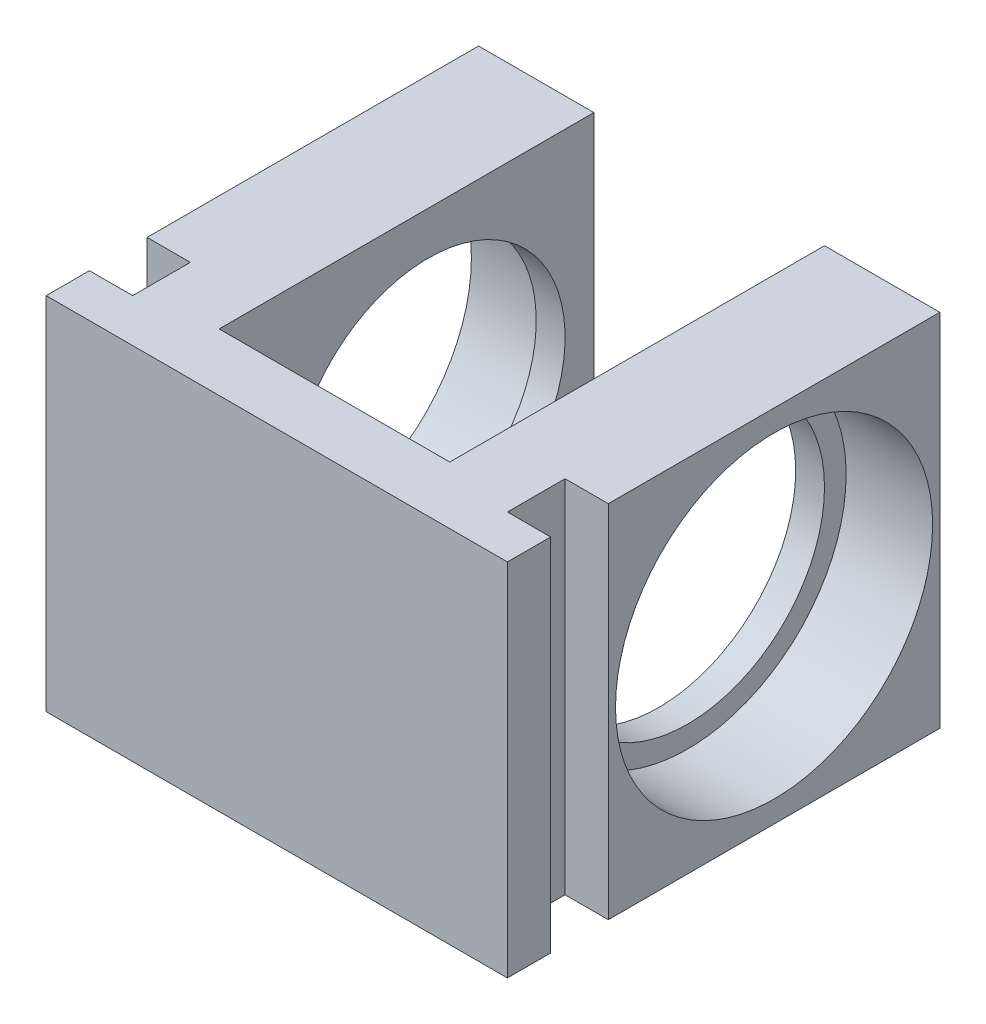
SolidWorks part; units mm, degrees
ref_plane "Ebene vorne" through (0, 0, 0) normal (0, 0, 1) x (1, 0, 0)
ref_plane "Ebene oben" through (0, 0, 0) normal (0, 1, 0) x (1, 0, 0)
ref_plane "Ebene rechts" through (0, 0, 0) normal (1, 0, 0) x (0, 0, -1)
sketch "Skizze1" plane through (0, 0, 0) normal (0, 1, 0) x (1, 0, 0)
  line L0 (0, 0) -> (0, 10.7327) construction
  line L1 (-8, 0) -> (-8, 26)
  line L2 (-8, 26) -> (-16, 26)
  line L3 (-16, 26) -> (-16, -4)
  line L4 (-16, -4) -> (16, -4)
  line L5 (16, 26) -> (16, -4)
  line L6 (8, 0) -> (-8, 0)
  line L7 (8, 26) -> (16, 26)
  line L8 (8, 0) -> (8, 26)
  point P10 (0, -4)
  dimension "D1" = 8
  dimension "D2" = 8
  dimension "D3" = 26
  dimension "D4" = 30
extrude "Aufsatz-Linear austragen1" add sketch "Skizze1" along normal blind 25
sketch "Skizze2" plane through (0, 0, 0) normal (0, -1, 0) x (1, 0, 0)
  line L0 (16, 4) -> (16, -26) construction
  line L1 (16, -3) -> (13, -3)
  line L2 (16, -3) -> (16, 1)
  line L3 (16, 1) -> (13, 1)
  line L4 (13, -3) -> (13, 1)
  line L5 (0, 0) -> (0, 4) construction
  line L6 (-16, 4) -> (16, 4) construction
  line L7 (-13, -3) -> (-13, 1)
  line L8 (-16, 1) -> (-13, 1)
  line L9 (-16, -3) -> (-16, 1)
  line L10 (-16, -3) -> (-13, -3)
  dimension "D1" = 4
  dimension "D2" = 3
  dimension "D3" = 3
extrude "Schnitt-Linear austragen1" cut sketch "Skizze2" against normal blind 25
sketch "Skizze3" plane through (-16, 0, 0) normal (-1, 0, 0) x (0, 0, 1)
  line L0 (-26, 12.5) -> (-3, 12.5) construction
  line L1 (-26, 25) -> (-26, 0) construction
  line L2 (-3, 25) -> (-3, 0) construction
  circle A0 centre (-14.5, 12.5) radius 9.5
  dimension "D1" = 19
extrude "Schnitt-Linear austragen2" cut sketch "Skizze3" against normal blind 35
sketch "Skizze4" plane through (-16, 0, 0) normal (-1, 0, 0) x (0, 0, 1)
  circle A0 centre (-14.5, 12.5) radius 11
  dimension "D1" = 22
extrude "Schnitt-Linear austragen3" cut sketch "Skizze4" against normal blind 6
sketch "Skizze5" plane through (16, 0, 0) normal (1, 0, 0) x (0, 0, -1)
  circle A0 centre (14.5, 12.5) radius 11
  dimension "D1" = 22
extrude "Schnitt-Linear austragen4" cut sketch "Skizze5" against normal blind 6
